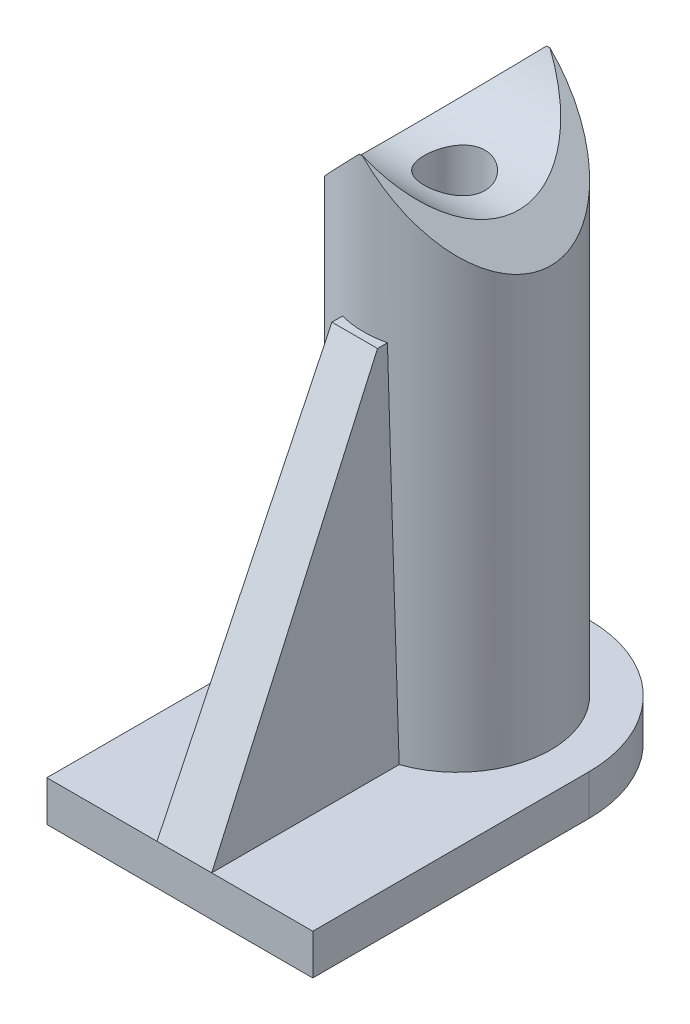
SolidWorks part; units mm, degrees
ref_plane "Front Plane" through (0, 0, 0) normal (0, 0, 1) x (1, 0, 0)
ref_plane "Top Plane" through (0, 0, 0) normal (0, 1, 0) x (1, 0, 0)
ref_plane "Right Plane" through (0, 0, 0) normal (1, 0, 0) x (0, 0, -1)
sketch "Sketch1" plane through (0, 0, 0) normal (0, 1, 0) x (1, 0, 0)
  line L1 (0, 0) -> (10.5, 0)
  line L2 (0, 0) -> (0, -16.1)
  line L3 (0, -16.1) -> (10.5, -16.1)
  line L4 (10.5, 0) -> (10.5, -16.1)
  dimension "D1" = 16.1
  dimension "D2" = 10.5
extrude "Boss-Extrude1" add sketch "Sketch1" along normal blind 1.6
fillet "Fillet1" radius 5.2 2 edges at (0, 0.8, 0) (10.5, 0.8, 0)
sketch "Sketch2" plane through (0, 1.6, 0) normal (0, 1, 0) x (1, 0, 0)
  circle A0 centre (5.2, -5.2) radius 3.7
  dimension "D1" = 7.4
extrude "Boss-Extrude2" add sketch "Sketch2" along normal blind 20.3
sketch "Sketch3" plane through (10.5, 0, 0) normal (1, 0, 0) x (0, 0, -1)
  circle A0 centre (-5.2, 23.4323) radius 4.0047
extrude "Cut-Extrude1" cut sketch "Sketch3" against normal blind 20.3
sketch "Sketch4" plane through (0, 1.6, 0) normal (0, 1, 0) x (1, 0, 0)
  line L0 (7.7906, -2.5583) -> (7.7906, -7.8417)
  arc A0 (7.7906, -7.8417) -> (7.7906, -2.5583) centre (5.2, -5.2) ccw
extrude "Cut-Extrude2" cut sketch "Sketch4" along normal through all from offset 14.8
sketch "Sketch5" plane through (0, 0, 16.1) normal (0, 0, 1) x (1, 0, 0)
  line L0 (5.3, 2.7251) -> (5.3, 23.2315) construction
  line L1 (6.8134, 19.4) -> (14.0852, 19.4) construction
  line L2 (8.9, 16.4) -> (7.7906, 16.4) construction
  line L3 (5.3, 21.959) -> (7.7906, 19.4)
  line L4 (7.7906, 20.4225) -> (7.7906, 16.4) construction
  line L5 (7.7906, 19.4) -> (9.8283, 21.3832)
  line L6 (9.8283, 21.3832) -> (4.5346, 26.8223)
  line L7 (5.3, 21.959) -> (1.5, 18.159)
  line L8 (1.5, 19.4276) -> (1.5, 1.6) construction
  line L9 (-0.1863, 21.959) -> (4.5346, 26.8223)
  line L10 (1.5, 18.159) -> (-0.1863, 21.959)
  dimension "D1" = 3
extrude "Cut-Extrude4" cut sketch "Sketch5" against normal blind 20.3
sketch "Sketch6" plane through (0, 0, 0) normal (0, -1, 0) x (-1, 0, 0)
  circle A0 centre (-5.3, -5.2) radius 2.275
  dimension "D1" = 4.55
extrude "Cut-Extrude5" cut sketch "Sketch6" against normal blind 16.3
chamfer "Chamfer1" distance 1 angle 45 1 edges at (5.3, 0, 2.925)
sketch "Sketch7" plane through (0, 16.3, 0) normal (0, -1, 0) x (1, 0, 0)
  circle A0 centre (5.3, 5.2) radius 1.2
  dimension "D1" = 2.4
extrude "Cut-Extrude6" cut sketch "Sketch7" against normal up to next
sketch "Sketch8" plane through (0, 0, 16.1) normal (0, 0, 1) x (1, 0, 0)
  line L0 (0, 1.6) -> (10.5, 1.6) construction
  line L1 (4.35, 15.9) -> (3.9912, 1.6)
  line L2 (3.9912, 1.6) -> (6.15, 1.6)
  line L3 (6.15, 15.9) -> (4.35, 15.9)
  line L4 (6.15, 1.6) -> (6.15, 15.9)
  point P0 (5.25, 1.6)
  dimension "D1" = 1.8
  dimension "D2" = 14.3
extrude "Boss-Extrude4" add sketch "Sketch8" against normal up to body
sketch "Sketch11" plane through (6.15, 0, 0) normal (1, 0, 0) x (0, 0, -1)
  line L0 (-16.1, 1.6) -> (-9.1935, 15.9)
  line L1 (-8.776, 15.9) -> (-16.1, 15.9) construction
  line L2 (-9.1935, 15.9) -> (-16.1, 15.9)
  line L3 (-16.1, 15.9) -> (-16.1, 1.6)
  line L4 (-16.1, 1.6) -> (-16.0643, 1.5418)
  line M3 (-8.776, 15.9) -> (-16.1, 15.9)
  line M4 (-16.1, 15.9) -> (-16.1, 1.6)
extrude "Cut-Extrude8" cut sketch "Sketch11" against normal up to next contours L0 M4 M3
mirror "Mirror3" about plane through (0, 1.6, 0) normal (1, 0, 0) of bodies 112
delete or keep bodies "Body-Delete1" type delete bodies bodies 112
